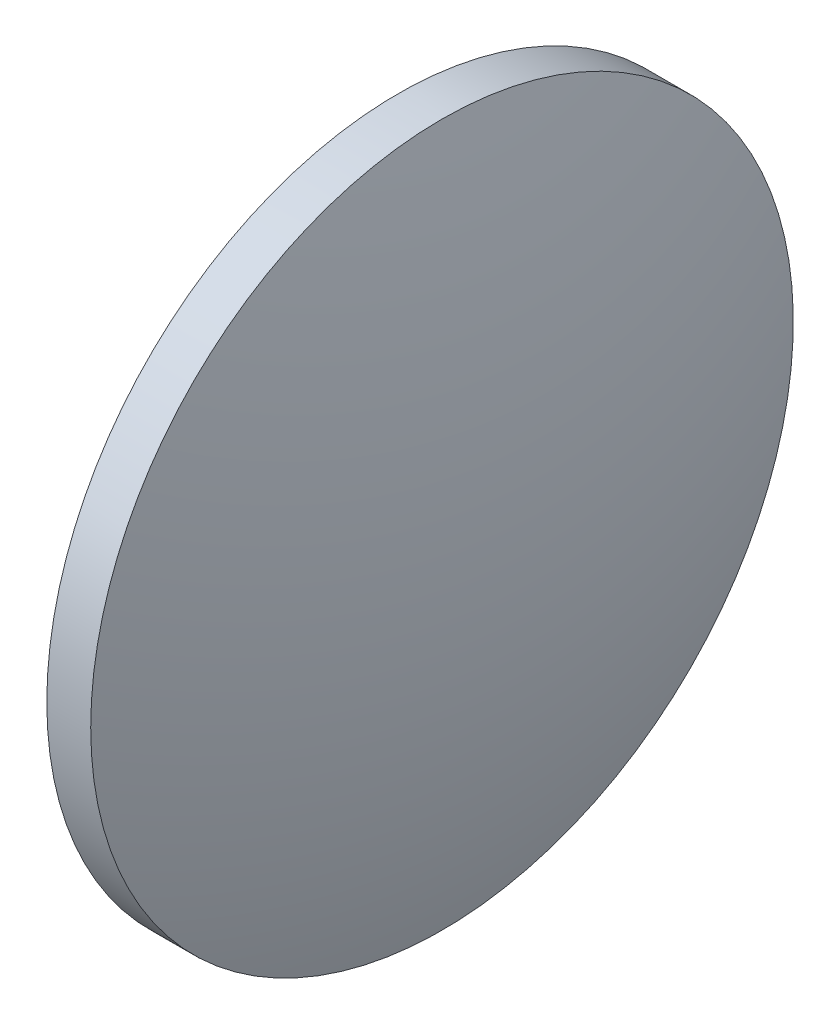
SolidWorks part; units mm, degrees
ref_plane "前视基准面" through (0, 0, 0) normal (0, 0, 1) x (1, 0, 0)
ref_plane "上视基准面" through (0, 0, 0) normal (0, 1, 0) x (1, 0, 0)
ref_plane "右视基准面" through (0, 0, 0) normal (1, 0, 0) x (0, 0, -1)
sketch "草图1" plane through (0, 0, 0) normal (0, 0, 1) x (1, 0, 0)
  line L0 (560.4465, 216.2327) -> (587.338, 216.2327) construction
  line L1 (569.953, 216.2327) -> (569.953, 236.2327)
  line L2 (575.633, 216.2327) -> (569.953, 216.2327)
  line L5 (569.953, 236.2327) -> (572.453, 236.2327)
  arc A0 (575.633, 216.2327) -> (572.453, 236.2327) centre (511.1499, 216.2327) ccw
revolve "旋转1" add sketch "草图1" angle 360 about L0
